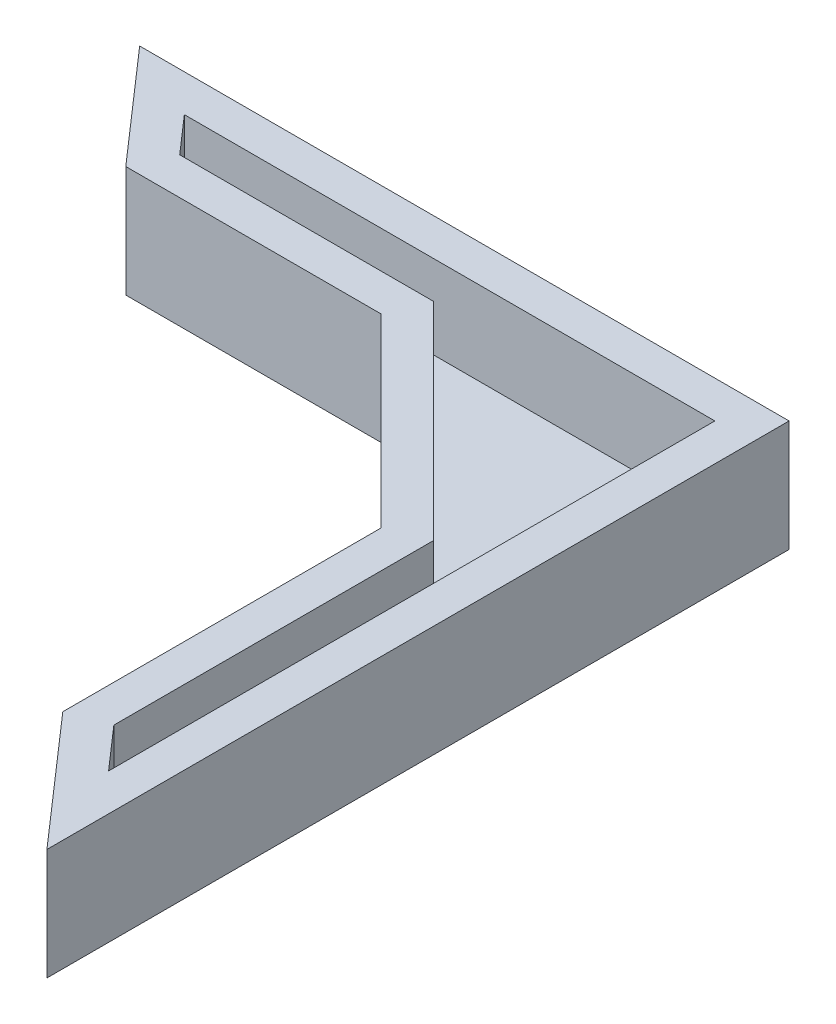
SolidWorks part; units mm, degrees
ref_plane "前视基准面" through (0, 0, 0) normal (0, 0, 1) x (1, 0, 0)
ref_plane "上视基准面" through (0, 0, 0) normal (0, 1, 0) x (1, 0, 0)
ref_plane "右视基准面" through (0, 0, 0) normal (1, 0, 0) x (0, 0, -1)
sketch "草图1" plane through (0, 0, 0) normal (0, 1, 0) x (1, 0, 0)
  line L0 (-35, 0) -> (0, 0)
  line L1 (0, 0) -> (0, -40)
  line L2 (0, -40) -> (-6, -33.1429)
  line L3 (-55, 0) -> (55, 0) construction
  line L4 (0, -55) -> (0, 55) construction
  line L5 (-29.75, -6) -> (-16, -6)
  line L6 (-6, -16) -> (-6, -33.1429)
  line L7 (-29.75, -6) -> (-35, 0)
  line L8 (-16, -6) -> (-6, -16)
  point P10 (0, -20)
  dimension "D1" = 35
  dimension "D2" = 40
  dimension "D3" = 6
  dimension "D4" = 6
  dimension "D5" = 45
extrude "凸台-拉伸1" add sketch "草图1" along normal blind 6
sketch "草图3" plane through (0, 6, 0) normal (0, 1, 0) x (1, 0, 0)
  line L0 (-30.5925, -2) -> (-28.8425, -4)
  line L1 (-28.8425, -4) -> (-15.1716, -4)
  line L2 (-15.1716, -4) -> (-4, -15.1716)
  line L3 (-4, -15.1716) -> (-4, -32.3914)
  line L4 (-4, -32.3914) -> (-2, -34.6771)
  line L5 (-2, -34.6771) -> (-2, -2)
  line L6 (-2, -2) -> (-30.5925, -2)
  line L8 (-16, -6) -> (-6, -16) construction
  line L9 (-29.75, -6) -> (-16, -6) construction
  line L10 (-35, 0) -> (-29.75, -6) construction
  line L11 (-6, -16) -> (-6, -33.1429) construction
  line L12 (-6, -33.1429) -> (0, -40) construction
  line L13 (-55, 0) -> (55, 0) construction
  line L14 (0, -55) -> (0, 55) construction
  dimension "D1" = 2
  dimension "D2" = 2
  dimension "D3" = 2
  dimension "D4" = 2
  dimension "D5" = 2
  dimension "D6" = 2
  dimension "D7" = 2
extrude "切除-拉伸1" cut sketch "草图3" against normal offset from surface (4.5 mm away) 1.5 up to face at (-13.25, 0, 14.449)
